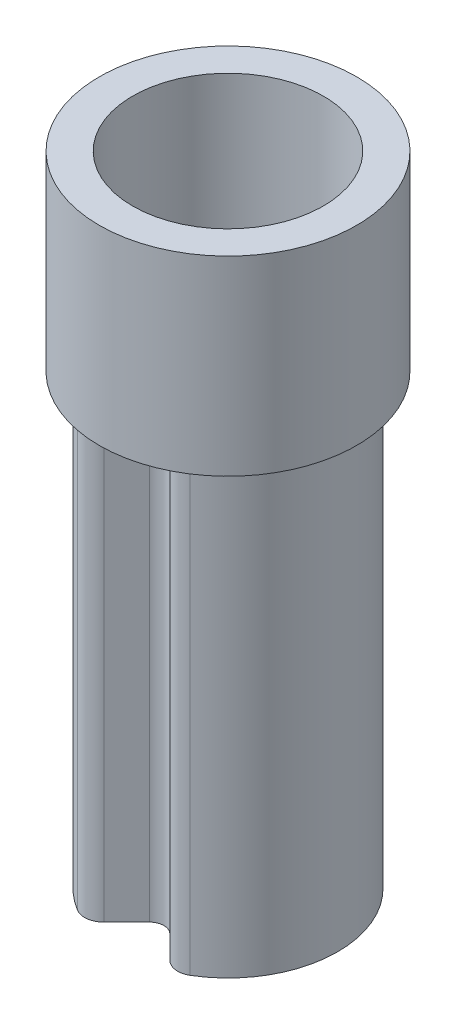
SolidWorks part; units mm, degrees
ref_plane "Front Plane" through (0, 0, 0) normal (0, 0, 1) x (1, 0, 0)
ref_plane "Top Plane" through (0, 0, 0) normal (0, 1, 0) x (1, 0, 0)
ref_plane "Right Plane" through (0, 0, 0) normal (1, 0, 0) x (0, 0, -1)
sketch "Sketch1" plane through (0, 0, 0) normal (0, 1, 0) x (1, 0, 0)
  line L0 (0, 0) -> (0, -1.15) construction
  line L1 (-0.4488, -1.0588) -> (-0.1061, -0.7161)
  line L2 (0.1061, -0.7161) -> (0.4488, -1.0588)
  line L3 (-0.4796, -0.8775) -> (-0.2121, -0.61)
  line L4 (0.2121, -0.61) -> (0.4796, -0.8775)
  arc A0 (0.4488, -1.0588) -> (-0.4488, -1.0588) centre (0, 0) ccw
  arc A1 (0.1061, -0.7161) -> (-0.1061, -0.7161) centre (0, -0.8221) ccw
  arc A2 (0.2121, -0.61) -> (-0.2121, -0.61) centre (0, -0.8221) ccw
  arc A3 (0.4796, -0.8775) -> (-0.4796, -0.8775) centre (0, 0) ccw
  point P8 (0, -0.61)
  dimension "D1" = 2.3
  dimension "D3" = 0.15
  dimension "D2" = 0.61
  dimension "D4" = 0.15
extrude "Boss-Extrude1" add sketch "Sketch1" along normal blind 4.7 contours A3 L3 A2 L4
fillet "Fillet1" radius 0.05 2 edges at (0.4796, 2.35, 0.8775) (-0.4796, 2.35, 0.8775)
fillet "Fillet2" radius 0.2 2 edges at (0.4488, 2.35, 1.0588) (-0.4488, 2.35, 1.0588)
sketch "Sketch2" plane through (0, 4.7, 0) normal (0, 1, 0) x (1, 0, 0)
  circle A0 centre (0, 0) radius 1.35
  circle A1 centre (0, 0) radius 1
  arc A2 (0.5136, -0.858) -> (-0.5136, -0.858) centre (0, 0) ccw construction
  dimension "D1" = 2.7
extrude "Boss-Extrude2" add sketch "Sketch2" along normal offset from surface (2 mm away) 6.7 up to face at (0, 0, 0.537)
